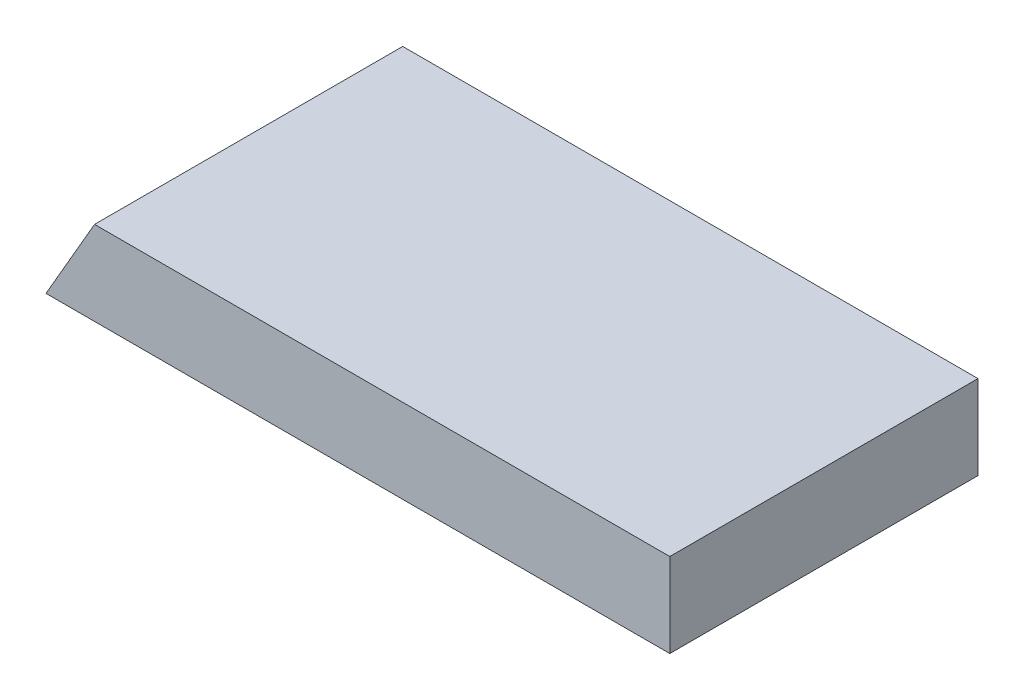
SolidWorks part; units mm, degrees
ref_plane "Front Plane" through (0, 0, 0) normal (0, 0, 1) x (1, 0, 0)
ref_plane "Top Plane" through (0, 0, 0) normal (0, 1, 0) x (1, 0, 0)
ref_plane "Right Plane" through (0, 0, 0) normal (1, 0, 0) x (0, 0, -1)
sketch "Sketch1" plane through (0, 0, 0) normal (0, 1, 0) x (1, 0, 0)
  line L1 (0, 0) -> (381, 0)
  line L2 (0, 0) -> (0, 139.7)
  line L3 (0, 139.7) -> (381, 139.7)
  line L4 (381, 0) -> (381, 139.7)
  dimension "D1" = 139.7
  dimension "D2" = 381
extrude "Boss-Extrude1" add sketch "Sketch1" along normal blind 38.1
sketch "Sketch2" plane through (0, 0, 0) normal (0, 0, 1) x (1, 0, 0)
  line L0 (98.2562, 0) -> (120.2532, 38.1)
  line L1 (0, 0) -> (381, 0) construction
  line L2 (120.2532, 38.1) -> (-111.2028, -362.7936) construction
  line L3 (0, 38.1) -> (381, 38.1) construction
  line L4 (120.2532, 38.1) -> (0, 38.1)
  line L5 (0, 38.1) -> (0, 0)
  line L6 (0, 0) -> (98.2562, 0)
extrude "Cut-Extrude2" cut sketch "Sketch2" against normal through all contours L6 L0 L4 L5
